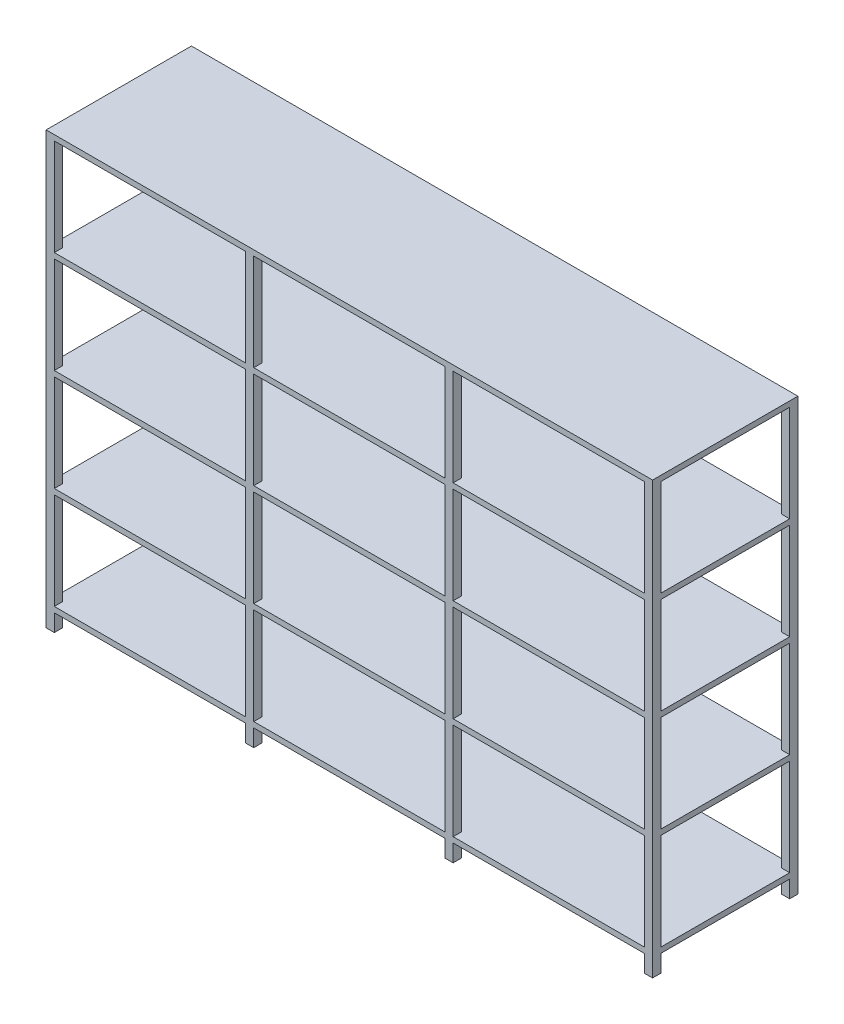
SolidWorks part; units mm, degrees
ref_plane "Alzado" through (0, 0, 0) normal (0, 0, 1) x (1, 0, 0)
ref_plane "Planta" through (0, 0, 0) normal (0, 1, 0) x (1, 0, 0)
ref_plane "Vista lateral" through (0, 0, 0) normal (1, 0, 0) x (0, 0, -1)
sketch "Croquis1" plane through (0, 0, 0) normal (0, 1, 0) x (1, 0, 0)
  line L0 (0, -38.1) -> (0, -338.1) construction
  line L1 (0, 0) -> (38.1, 0)
  line L2 (0, 0) -> (0, -38.1)
  line L3 (0, -38.1) -> (38.1, -38.1)
  line L4 (38.1, 0) -> (38.1, -38.1)
  line L5 (38.1, 0) -> (928.1, 0) construction
  line L6 (966.2, 0) -> (1856.2, 0) construction
  line L7 (928.1, 0) -> (966.2, 0)
  line L8 (928.1, 0) -> (928.1, -38.1)
  line L9 (928.1, -38.1) -> (966.2, -38.1)
  line L10 (966.2, 0) -> (966.2, -38.1)
  line L11 (1894.3, 0) -> (2784.3, 0) construction
  line L12 (1856.2, 0) -> (1894.3, 0)
  line L13 (1856.2, 0) -> (1856.2, -38.1)
  line L14 (1856.2, -38.1) -> (1894.3, -38.1)
  line L15 (1894.3, 0) -> (1894.3, -38.1)
  line L16 (0, -338.1) -> (218.5329, -338.1) construction
  line L17 (2784.3, 0) -> (2822.4, 0)
  line L18 (2784.3, 0) -> (2784.3, -38.1)
  line L19 (2784.3, -38.1) -> (2822.4, -38.1)
  line L20 (2822.4, 0) -> (2822.4, -38.1)
  line L21 (1894.3, -676.2) -> (2784.3, -676.2) construction
  line L22 (966.2, -676.2) -> (1856.2, -676.2) construction
  line L23 (38.1, -676.2) -> (928.1, -676.2) construction
  line L24 (2822.4, -676.2) -> (2822.4, -638.1)
  line L25 (2784.3, -638.1) -> (2822.4, -638.1)
  line L26 (2784.3, -676.2) -> (2784.3, -638.1)
  line L27 (2784.3, -676.2) -> (2822.4, -676.2)
  line L28 (1894.3, -676.2) -> (1894.3, -638.1)
  line L29 (1856.2, -638.1) -> (1894.3, -638.1)
  line L30 (1856.2, -676.2) -> (1856.2, -638.1)
  line L31 (1856.2, -676.2) -> (1894.3, -676.2)
  line L32 (966.2, -676.2) -> (966.2, -638.1)
  line L33 (928.1, -638.1) -> (966.2, -638.1)
  line L34 (928.1, -676.2) -> (928.1, -638.1)
  line L35 (928.1, -676.2) -> (966.2, -676.2)
  line L36 (38.1, -676.2) -> (38.1, -638.1)
  line L37 (0, -638.1) -> (38.1, -638.1)
  line L38 (0, -676.2) -> (0, -638.1)
  line L39 (0, -676.2) -> (38.1, -676.2)
  dimension "D1" = 38.1
  dimension "D2" = 38.1
  dimension "D3" = 300
  dimension "D4" = 890
  dimension "D5" = 38.1
  dimension "D6" = 38.1
  dimension "D7" = 890
  dimension "D8" = 38.1
  dimension "D9" = 38.1
  dimension "D10" = 890
  dimension "D11" = 38.1
  dimension "D12" = 38.1
extrude "Saliente-Extruir1" add sketch "Croquis1" along normal blind 80
sketch "Croquis2" plane through (0, 80, 0) normal (0, 1, 0) x (1, 0, 0)
  line L1 (0, 0) -> (2822.4, 0)
  line L2 (0, 0) -> (0, -676.2)
  line L3 (0, -676.2) -> (2822.4, -676.2)
  line L4 (2822.4, 0) -> (2822.4, -676.2)
extrude "Saliente-Extruir2" add sketch "Croquis2" along normal blind 25.4
sketch "Croquis3" plane through (0, 105.4, 0) normal (0, 1, 0) x (1, 0, 0)
  line L1 (38.1, -38.1) -> (0, -38.1)
  line L2 (38.1, -38.1) -> (38.1, 0)
  line L3 (38.1, 0) -> (0, 0)
  line L4 (0, -38.1) -> (0, 0)
  line L5 (928.1, 0) -> (966.2, 0)
  line L6 (928.1, 0) -> (928.1, -38.1)
  line L7 (928.1, -38.1) -> (966.2, -38.1)
  line L8 (966.2, 0) -> (966.2, -38.1)
  line L9 (1856.2, 0) -> (1894.3, 0)
  line L10 (1856.2, 0) -> (1856.2, -38.1)
  line L11 (1856.2, -38.1) -> (1894.3, -38.1)
  line L12 (1894.3, 0) -> (1894.3, -38.1)
  line L13 (2784.3, 0) -> (2822.4, 0)
  line L14 (2784.3, 0) -> (2784.3, -38.1)
  line L15 (2784.3, -38.1) -> (2822.4, -38.1)
  line L16 (2822.4, 0) -> (2822.4, -38.1)
  line L17 (2784.3, -638.1) -> (2822.4, -638.1)
  line L18 (2784.3, -638.1) -> (2784.3, -676.2)
  line L19 (2784.3, -676.2) -> (2822.4, -676.2)
  line L20 (2822.4, -638.1) -> (2822.4, -676.2)
  line L21 (1856.2, -638.1) -> (1894.3, -638.1)
  line L22 (1856.2, -638.1) -> (1856.2, -676.2)
  line L23 (1856.2, -676.2) -> (1894.3, -676.2)
  line L24 (1894.3, -638.1) -> (1894.3, -676.2)
  line L25 (928.1, -638.1) -> (966.2, -638.1)
  line L26 (928.1, -638.1) -> (928.1, -676.2)
  line L27 (928.1, -676.2) -> (966.2, -676.2)
  line L28 (966.2, -638.1) -> (966.2, -676.2)
  line L29 (0, -638.1) -> (38.1, -638.1)
  line L30 (0, -638.1) -> (0, -676.2)
  line L31 (0, -676.2) -> (38.1, -676.2)
  line L32 (38.1, -638.1) -> (38.1, -676.2)
extrude "Saliente-Extruir3" add sketch "Croquis3" along normal blind 450
sketch "Croquis4" plane through (0, 555.4, 0) normal (0, 1, 0) x (1, 0, 0)
  line L1 (0, 0) -> (2822.4, 0)
  line L2 (0, 0) -> (0, -676.2)
  line L3 (0, -676.2) -> (2822.4, -676.2)
  line L4 (2822.4, 0) -> (2822.4, -676.2)
extrude "Saliente-Extruir4" add sketch "Croquis4" along normal blind 25.4
sketch "Croquis5" plane through (0, 580.8, 0) normal (0, 1, 0) x (1, 0, 0)
  line L1 (0, 0) -> (38.1, 0)
  line L2 (0, 0) -> (0, -38.1)
  line L3 (0, -38.1) -> (38.1, -38.1)
  line L4 (38.1, 0) -> (38.1, -38.1)
  line L5 (928.1, 0) -> (966.2, 0)
  line L6 (928.1, 0) -> (928.1, -38.1)
  line L7 (928.1, -38.1) -> (966.2, -38.1)
  line L8 (966.2, 0) -> (966.2, -38.1)
  line L9 (1856.2, 0) -> (1894.3, 0)
  line L10 (1856.2, 0) -> (1856.2, -38.1)
  line L11 (1856.2, -38.1) -> (1894.3, -38.1)
  line L12 (1894.3, 0) -> (1894.3, -38.1)
  line L13 (2784.3, 0) -> (2822.4, 0)
  line L14 (2784.3, 0) -> (2784.3, -38.1)
  line L15 (2784.3, -38.1) -> (2822.4, -38.1)
  line L16 (2822.4, 0) -> (2822.4, -38.1)
  line L17 (2784.3, -638.1) -> (2822.4, -638.1)
  line L18 (2784.3, -638.1) -> (2784.3, -676.2)
  line L19 (2784.3, -676.2) -> (2822.4, -676.2)
  line L20 (2822.4, -638.1) -> (2822.4, -676.2)
  line L21 (1856.2, -638.1) -> (1894.3, -638.1)
  line L22 (1856.2, -638.1) -> (1856.2, -676.2)
  line L23 (1856.2, -676.2) -> (1894.3, -676.2)
  line L24 (1894.3, -638.1) -> (1894.3, -676.2)
  line L25 (928.1, -638.1) -> (966.2, -638.1)
  line L26 (928.1, -638.1) -> (928.1, -676.2)
  line L27 (928.1, -676.2) -> (966.2, -676.2)
  line L28 (966.2, -638.1) -> (966.2, -676.2)
  line L29 (0, -638.1) -> (38.1, -638.1)
  line L30 (0, -638.1) -> (0, -676.2)
  line L31 (0, -676.2) -> (38.1, -676.2)
  line L32 (38.1, -638.1) -> (38.1, -676.2)
extrude "Saliente-Extruir5" add sketch "Croquis5" along normal blind 450
sketch "Croquis6" plane through (0, 1030.8, 0) normal (0, 1, 0) x (1, 0, 0)
  line L1 (0, 0) -> (2822.4, 0)
  line L2 (0, 0) -> (0, -676.2)
  line L3 (0, -676.2) -> (2822.4, -676.2)
  line L4 (2822.4, 0) -> (2822.4, -676.2)
extrude "Saliente-Extruir6" add sketch "Croquis6" along normal blind 25.4
sketch "Croquis7" plane through (0, 1056.2, 0) normal (0, 1, 0) x (1, 0, 0)
  line L1 (38.1, -38.1) -> (0, -38.1)
  line L2 (38.1, -38.1) -> (38.1, 0)
  line L3 (38.1, 0) -> (0, 0)
  line L4 (0, -38.1) -> (0, 0)
  line L5 (966.2, -38.1) -> (928.1, -38.1)
  line L6 (966.2, -38.1) -> (966.2, 0)
  line L7 (966.2, 0) -> (928.1, 0)
  line L8 (928.1, -38.1) -> (928.1, 0)
  line L9 (1894.3, -38.1) -> (1856.2, -38.1)
  line L10 (1894.3, -38.1) -> (1894.3, 0)
  line L11 (1894.3, 0) -> (1856.2, 0)
  line L12 (1856.2, -38.1) -> (1856.2, 0)
  line L13 (2822.4, -38.1) -> (2784.3, -38.1)
  line L14 (2822.4, -38.1) -> (2822.4, 0)
  line L15 (2822.4, 0) -> (2784.3, 0)
  line L16 (2784.3, -38.1) -> (2784.3, 0)
  line L17 (2784.3, -638.1) -> (2822.4, -638.1)
  line L18 (2784.3, -638.1) -> (2784.3, -676.2)
  line L19 (2784.3, -676.2) -> (2822.4, -676.2)
  line L20 (2822.4, -638.1) -> (2822.4, -676.2)
  line L21 (1856.2, -638.1) -> (1894.3, -638.1)
  line L22 (1856.2, -638.1) -> (1856.2, -676.2)
  line L23 (1856.2, -676.2) -> (1894.3, -676.2)
  line L24 (1894.3, -638.1) -> (1894.3, -676.2)
  line L25 (928.1, -638.1) -> (966.2, -638.1)
  line L26 (928.1, -638.1) -> (928.1, -676.2)
  line L27 (928.1, -676.2) -> (966.2, -676.2)
  line L28 (966.2, -638.1) -> (966.2, -676.2)
  line L29 (0, -638.1) -> (38.1, -638.1)
  line L30 (0, -638.1) -> (0, -676.2)
  line L31 (0, -676.2) -> (38.1, -676.2)
  line L32 (38.1, -638.1) -> (38.1, -676.2)
extrude "Saliente-Extruir7" add sketch "Croquis7" along normal blind 450
sketch "Croquis8" plane through (0, 1506.2, 0) normal (0, 1, 0) x (1, 0, 0)
  line L1 (0, 0) -> (2822.4, 0)
  line L2 (0, 0) -> (0, -676.2)
  line L3 (0, -676.2) -> (2822.4, -676.2)
  line L4 (2822.4, 0) -> (2822.4, -676.2)
extrude "Saliente-Extruir8" add sketch "Croquis8" along normal blind 25.4
sketch "Croquis9" plane through (0, 1531.6, 0) normal (0, 1, 0) x (1, 0, 0)
  line L1 (0, 0) -> (38.1, 0)
  line L2 (0, 0) -> (0, -38.1)
  line L3 (0, -38.1) -> (38.1, -38.1)
  line L4 (38.1, 0) -> (38.1, -38.1)
  line L5 (928.1, 0) -> (966.2, 0)
  line L6 (928.1, 0) -> (928.1, -38.1)
  line L7 (928.1, -38.1) -> (966.2, -38.1)
  line L8 (966.2, 0) -> (966.2, -38.1)
  line L9 (1856.2, 0) -> (1894.3, 0)
  line L10 (1856.2, 0) -> (1856.2, -38.1)
  line L11 (1856.2, -38.1) -> (1894.3, -38.1)
  line L12 (1894.3, 0) -> (1894.3, -38.1)
  line L13 (2784.3, 0) -> (2822.4, 0)
  line L14 (2784.3, 0) -> (2784.3, -38.1)
  line L15 (2784.3, -38.1) -> (2822.4, -38.1)
  line L16 (2822.4, 0) -> (2822.4, -38.1)
  line L17 (2784.3, -638.1) -> (2822.4, -638.1)
  line L18 (2784.3, -638.1) -> (2784.3, -676.2)
  line L19 (2784.3, -676.2) -> (2822.4, -676.2)
  line L20 (2822.4, -638.1) -> (2822.4, -676.2)
  line L21 (1856.2, -638.1) -> (1894.3, -638.1)
  line L22 (1856.2, -638.1) -> (1856.2, -676.2)
  line L23 (1856.2, -676.2) -> (1894.3, -676.2)
  line L24 (1894.3, -638.1) -> (1894.3, -676.2)
  line L25 (928.1, -638.1) -> (966.2, -638.1)
  line L26 (928.1, -638.1) -> (928.1, -676.2)
  line L27 (928.1, -676.2) -> (966.2, -676.2)
  line L28 (966.2, -638.1) -> (966.2, -676.2)
  line L29 (0, -638.1) -> (38.1, -638.1)
  line L30 (0, -638.1) -> (0, -676.2)
  line L31 (0, -676.2) -> (38.1, -676.2)
  line L32 (38.1, -638.1) -> (38.1, -676.2)
extrude "Saliente-Extruir9" add sketch "Croquis9" along normal blind 450
sketch "Croquis10" plane through (0, 1981.6, 0) normal (0, 1, 0) x (1, 0, 0)
  line L1 (0, 0) -> (2822.4, 0)
  line L2 (0, 0) -> (0, -676.2)
  line L3 (0, -676.2) -> (2822.4, -676.2)
  line L4 (2822.4, 0) -> (2822.4, -676.2)
extrude "Saliente-Extruir10" add sketch "Croquis10" along normal blind 25.4
